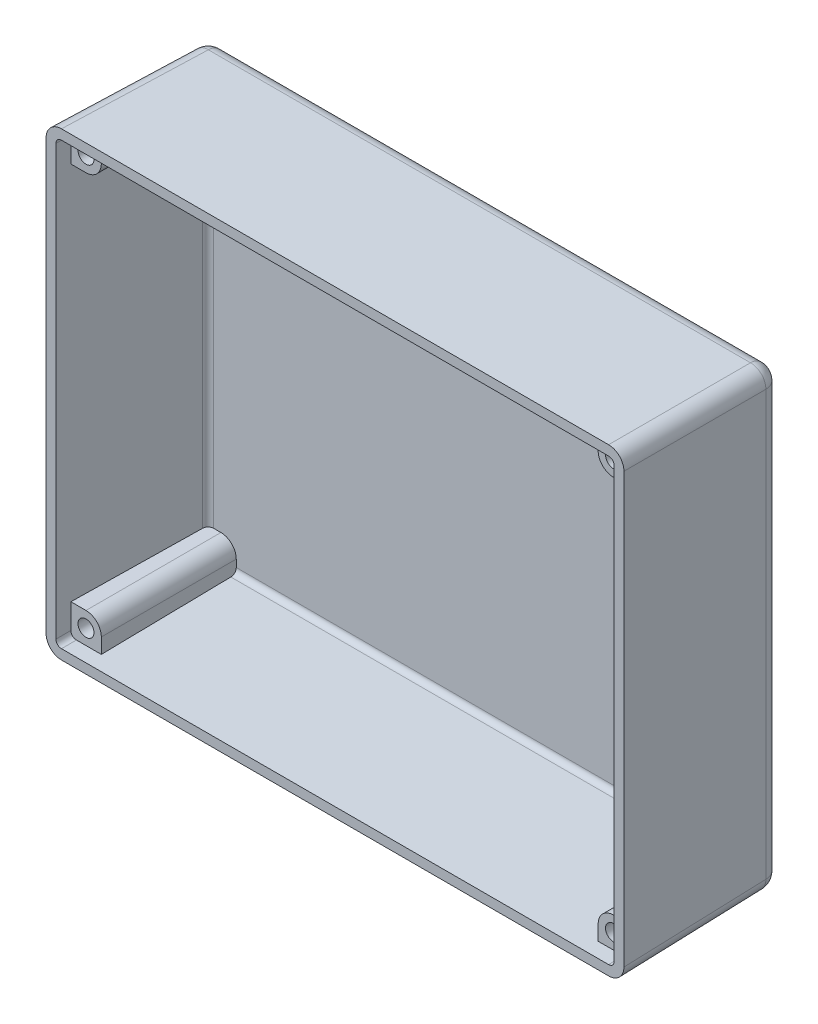
SolidWorks part; units mm, degrees
ref_plane "Front Plane" through (0, 0, 0) normal (0, 0, 1) x (1, 0, 0)
ref_plane "Top Plane" through (0, 0, 0) normal (0, 1, 0) x (1, 0, 0)
ref_plane "Right Plane" through (0, 0, 0) normal (1, 0, 0) x (0, 0, -1)
sketch "Sketch1" plane through (0, 0, 0) normal (0, 0, 1) x (1, 0, 0)
  line L1 (0, 0) -> (119.634, 0)
  line L2 (0, 0) -> (0, 95.25)
  line L3 (0, 95.25) -> (119.634, 95.25)
  line L4 (119.634, 0) -> (119.634, 95.25)
  dimension "D1" = 95.25
  dimension "D2" = 119.634
extrude "Boss-Extrude1" add sketch "Sketch1" against normal blind 33.02 draft 1
fillet "Fillet1" radius 3.175 8 edges at (59.817, 0.5764, -33.02) (119.0576, 47.625, -33.02) (59.817, 94.6736, -33.02) (0.5764, 47.625, -33.02) (119.3458, 0.2882, -16.51) (0.2882, 0.2882, -16.51) (119.3458, 94.9618, -16.51) (0.2882, 94.9618, -16.51)
shell "Shell1" thickness 2.032
sketch "Sketch2" plane through (0, 0, -30.988) normal (0, 0, 1) x (1, 0, 0)
  line L0 (2.0323, 86.8677) -> (5.2073, 86.8677)
  line L1 (2.0323, 92.0749) -> (2.0323, 3.1751) construction
  line L2 (8.3823, 90.0427) -> (8.3823, 93.2177)
  line L3 (116.4589, 93.2177) -> (3.1751, 93.2177) construction
  line L4 (8.3823, 93.2177) -> (3.1751, 93.2177)
  line L5 (2.0323, 86.8677) -> (2.0323, 92.0749)
  line L6 (111.2517, 93.2177) -> (111.2517, 90.0427)
  line L7 (114.4267, 86.8677) -> (117.6017, 86.8677)
  line L8 (117.6017, 3.1751) -> (117.6017, 92.0749) construction
  line L9 (117.6017, 86.8677) -> (117.6017, 92.0749)
  line L10 (111.2517, 93.2177) -> (116.4589, 93.2177)
  line L11 (3.1751, 2.0323) -> (116.4589, 2.0323) construction
  line L12 (116.4589, 2.0323) -> (111.2517, 2.0323)
  line L13 (111.2517, 2.0323) -> (111.2517, 5.2073)
  line L14 (114.4267, 8.3823) -> (117.6017, 8.3823)
  line L15 (117.6017, 8.3823) -> (117.6017, 3.1751)
  line L16 (2.0323, 3.1751) -> (2.0323, 8.3823)
  line L17 (2.0323, 8.3823) -> (5.2073, 8.3823)
  line L18 (8.3823, 5.2073) -> (8.3823, 2.0323)
  line L19 (8.3823, 2.0323) -> (3.1751, 2.0323)
  arc A0 (2.0323, 92.0749) -> (3.1751, 93.2177) centre (3.1751, 92.0749) cw
  arc A1 (5.2073, 86.8677) -> (8.3823, 90.0427) centre (5.2073, 90.0427) ccw
  arc A2 (117.6017, 92.0749) -> (116.4589, 93.2177) centre (116.4589, 92.0749) ccw
  arc A3 (114.4267, 86.8677) -> (111.2517, 90.0427) centre (114.4267, 90.0427) cw
  arc A4 (117.6017, 3.1751) -> (116.4589, 2.0323) centre (116.4589, 3.1751) cw
  arc A5 (111.2517, 5.2073) -> (114.4267, 8.3823) centre (114.4267, 5.2073) cw
  arc A6 (3.1751, 2.0323) -> (2.0323, 3.1751) centre (3.1751, 3.1751) cw
  arc A7 (5.2073, 8.3823) -> (8.3823, 5.2073) centre (5.2073, 5.2073) cw
  point P14 (8.3823, 86.8677)
  point P27 (111.2517, 86.8677)
  point P40 (111.2517, 8.3823)
  point P53 (8.3823, 8.3823)
  dimension "D3" = 3.175
  dimension "D6" = 3.175
  dimension "D9" = 3.175
  dimension "D12" = 3.175
  dimension "D1" = 6.35
  dimension "D2" = 6.35
  dimension "D4" = 6.35
  dimension "D5" = 6.35
  dimension "D7" = 6.35
  dimension "D8" = 6.35
  dimension "D10" = 6.35
  dimension "D11" = 6.35
extrude "Boss-Extrude2" add sketch "Sketch2" along normal blind 27.94
hole_wizard "Tap Drill for M4x0.7 Tap1" positions "Sketch4" profile "Sketch5" hole size "M4x0.7" standard "ANSI Metric"
sketch "Sketch4" plane through (0, 0, -3.048) normal (0, 0, 1) x (1, 0, 0)
  point P0 (5.2073, 90.0427)
  point P3 (114.4267, 90.0427)
  point P6 (114.4267, 5.2073)
  point P9 (5.2073, 5.2073)
sketch "Sketch5" plane through (5.2073, 90.0427, -3.048) normal (1, 0, 0) x (0, -1, 0)
  line L0 (0, 0) -> (0, 26.3914)
  line L1 (0, 26.3914) -> (1.65, 25.4)
  line L2 (1.65, 25.4) -> (1.65, 0)
  line L5 (1.65, 0) -> (0, 0)
  line L10 (0, 26.3914) -> (-1.65, 25.4) construction
  line L11 (0, -6.35) -> (0, 107.95) construction
  dimension "Hole Dia." = 3.3
  dimension "Hole Depth" = 25.4
  dimension "Drill Angle" = 118
